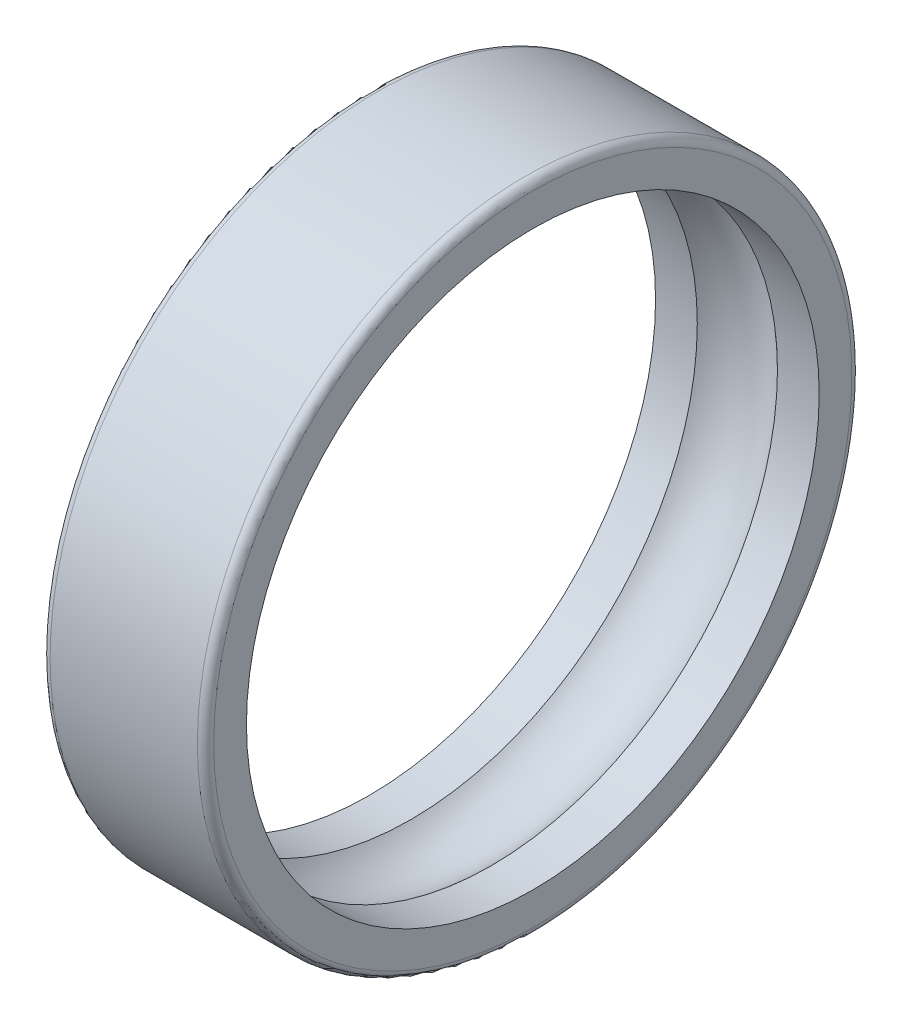
SolidWorks part; units mm, degrees
ref_plane "Plane1" through (0, 0, 0) normal (0, 0, 1) x (1, 0, 0)
ref_plane "Plane2" through (0, 0, 0) normal (0, 1, 0) x (1, 0, 0)
ref_plane "Plane3" through (0, 0, 0) normal (1, 0, 0) x (0, 0, -1)
sketch "Esquisse1" plane through (0, 0, 0) normal (0, 0, 1) x (1, 0, 0)
  line L0 (0, 7) -> (1.0202, 7) construction
  line L1 (0, 7.8) -> (0, 7) construction
  line L2 (0.2, 8) -> (3.8, 8) construction
  line L3 (4, 7) -> (4, 7.8) construction
  line L4 (2.9798, 7) -> (4, 7) construction
  line L5 (0, 7) -> (1.0202, 7)
  line L6 (0, 7.8) -> (0, 7)
  line L7 (0.2, 8) -> (3.8, 8)
  line L8 (4, 7) -> (4, 7.8)
  line L9 (2.9798, 7) -> (4, 7)
  line L10 (0, 0) -> (28.3481, 0) construction
  line L11 (0, 0) -> (37.6531, 0) construction
  arc A0 (0.2, 8) -> (0, 7.8) centre (0.2, 7.8) ccw construction
  arc A1 (4, 7.8) -> (3.8, 8) centre (3.8, 7.8) ccw construction
  circle A2 centre (2, 6) radius 1.4 construction
  arc A3 (0.2, 8) -> (0, 7.8) centre (0.2, 7.8) ccw
  arc A4 (4, 7.8) -> (3.8, 8) centre (3.8, 7.8) ccw
  arc A5 (2.9798, 7) -> (1.0202, 7) centre (2, 6) ccw
revolve "Base-Révolution" add sketch "Esquisse1" angle 360 about L10
